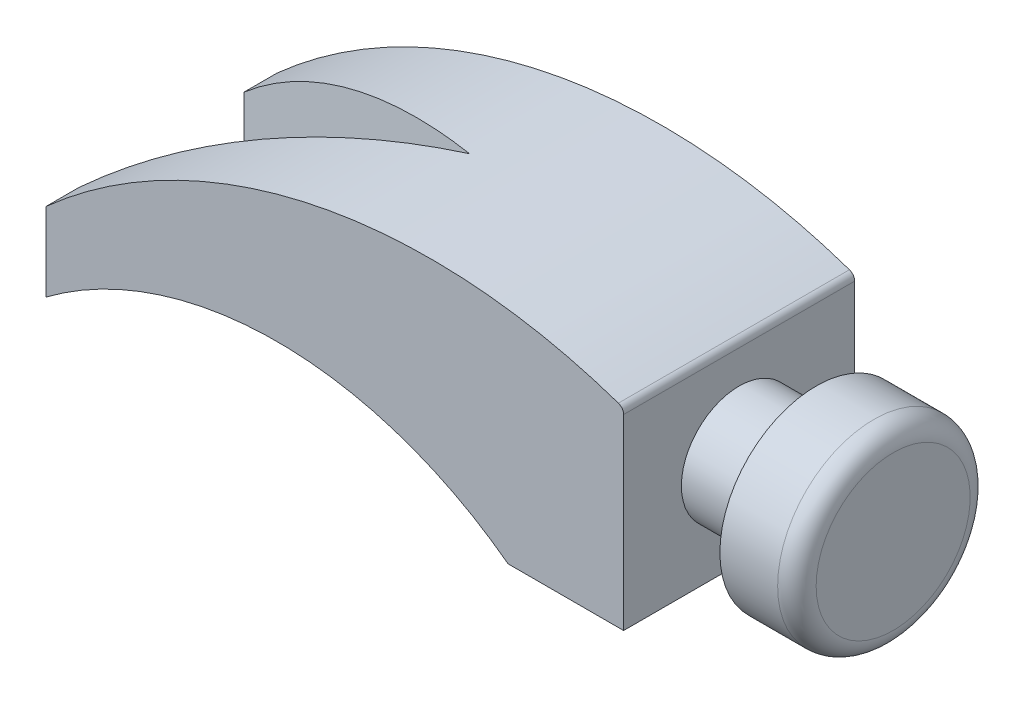
SolidWorks part; units mm, degrees
ref_plane "Ön Düzlem" through (0, 0, 0) normal (0, 0, 1) x (1, 0, 0)
ref_plane "Üst Düzlem" through (0, 0, 0) normal (0, 1, 0) x (1, 0, 0)
ref_plane "Sağ Düzlem" through (0, 0, 0) normal (1, 0, 0) x (0, 0, -1)
sketch "Çizim2" plane through (0, 0, 0) normal (0, 1, 0) x (1, 0, 0)
  line L0 (0, 30) -> (0, -30)
  line L1 (0, 30) -> (-150, 30)
  line L2 (0, 0) -> (-170.8046, 0) construction
  line L3 (0, -30) -> (-150, -30)
  line L4 (-150, 30) -> (-150, 21.4359)
  line L5 (-150, -30) -> (-150, -21.4359)
  line L6 (-150, 21.4359) -> (-70, 0)
  line L7 (-150, -21.4359) -> (-70, 0)
  point P4 (0, 0)
  point P9 (-150, 19.4253)
  dimension "D1" = 60
  dimension "D2" = 150
  dimension "D3" = 30
  dimension "D4" = 80
extrude "Yükseklik-Ekstrüzyon2" add sketch "Çizim2" along normal mid plane 60
sketch "Çizim3" plane through (0, 0, 30) normal (0, 0, 1) x (1, 0, 0)
  line L0 (-150, -30) -> (-30, -30)
  line L1 (-150, -30) -> (0, -30) construction
  arc A0 (-30, -30) -> (-150, -30) centre (-90, -110) ccw
  dimension "D2" = 100
  dimension "D1" = 120
extrude "Kes-Ekstrüzyon1" cut sketch "Çizim3" against normal up to next
sketch "Çizim5" plane through (0, 0, 0) normal (0, 0, 1) x (1, 0, 0)
  line L0 (0, 30) -> (0, 20)
  line L2 (0, 30) -> (0, -30) construction
  line L3 (0, -5) -> (114.7951, -5) construction
  line L5 (0, -20) -> (20, -20)
  line L6 (20, -20) -> (20, -30)
  line L7 (20, -30) -> (35, -30)
  line L8 (40, -25) -> (40, -5)
  line L10 (0, -5) -> (0, -20)
  line L11 (0, -5) -> (40, -5)
  arc A0 (35, -30) -> (40, -25) centre (35, -25) ccw
  point P18 (40, -30)
  dimension "D7" = 5
  dimension "D1" = 10
  dimension "D2" = 25
  dimension "D3" = 15
  dimension "D4" = 20
  dimension "D5" = 10
  dimension "D6" = 20
revolve "Döndür1" add sketch "Çizim5" angle 360 about L3
sketch "Çizim6" plane through (0, 0, 30) normal (0, 0, 1) x (1, 0, 0)
  line L0 (0, 30) -> (0, 20) construction
  line L1 (0, 30) -> (0, -30) construction
  line L2 (-150, 30) -> (-150, -30) construction
  line L3 (40, -25) -> (40, 15) construction
  line L4 (-150, -9.618) -> (-150, 30)
  line L5 (-150, 30) -> (0, 30)
  line L6 (0, 30) -> (0, 20)
  arc A0 (0, 20) -> (-150, -9.618) centre (-50, -121.4214) ccw
  dimension "D2" = 150
  dimension "D1" = 10
  dimension "D3" = 90
extrude "Kes-Ekstrüzyon2" cut sketch "Çizim6" against normal up to next
fillet "Radyus1" radius 2 1 edges at (0, 20, 0)
